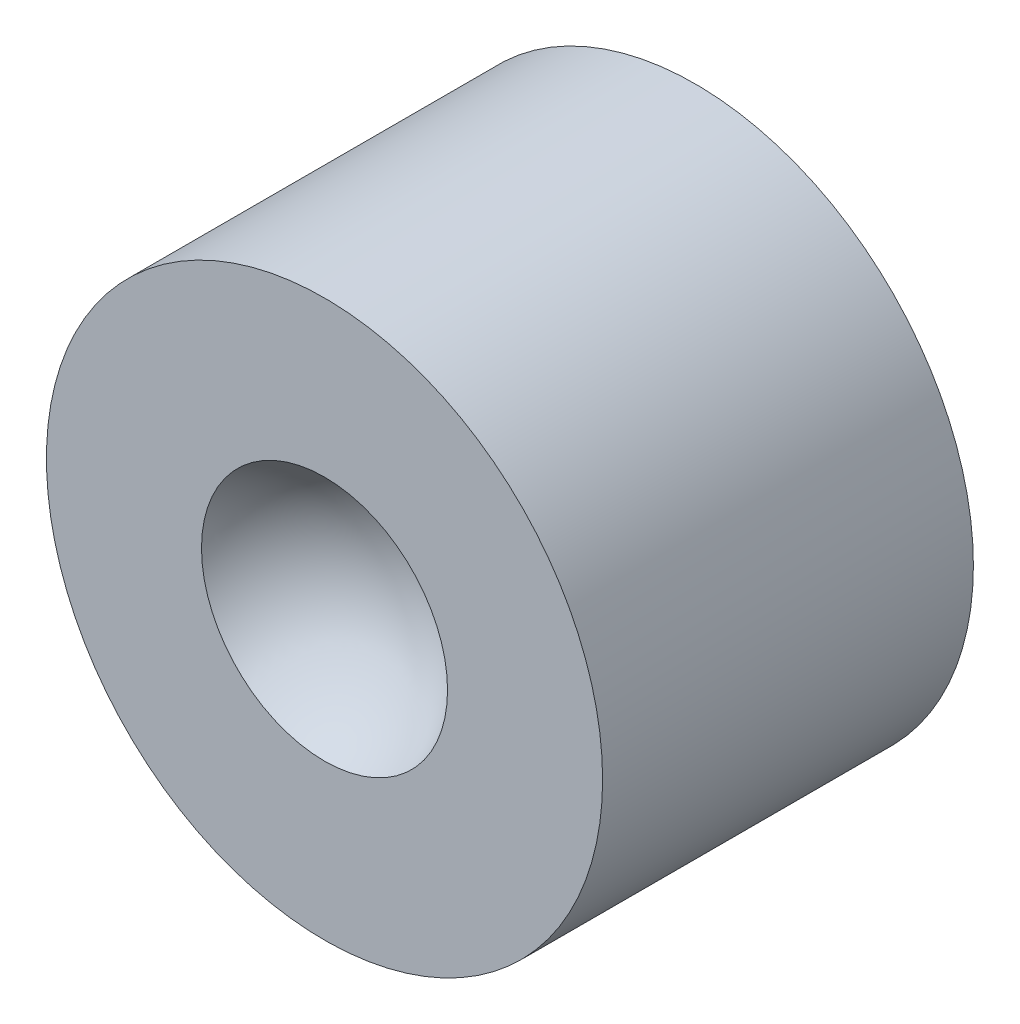
SolidWorks part; units mm, degrees
material "Brass"
ref_plane "Front Plane" through (0, 0, 0) normal (0, 0, 1) x (1, 0, 0)
ref_plane "Top Plane" through (0, 0, 0) normal (0, 1, 0) x (1, 0, 0)
ref_plane "Right Plane" through (0, 0, 0) normal (1, 0, 0) x (0, 0, -1)
sketch "Sketch1" plane through (0, 0, 0) normal (0, 0, 1) x (1, 0, 0)
  circle A0 centre (0, 0) radius 4.7625
  dimension "D1" = 9.525
extrude "Boss-Extrude1" add sketch "Sketch1" along normal blind 6.35
sketch "Sketch3" plane through (0, 0, 0) normal (0, 1, 0) x (1, 0, 0)
  line L0 (0, 0) -> (0, -6.721) construction
  line L1 (0, -6.35) -> (0, -5.08)
  line L2 (-4.7625, -6.35) -> (4.7625, -6.35) construction
  line L3 (2.1069, -6.35) -> (0, -6.35)
  arc A0 (0, -5.08) -> (2.1069, -6.35) centre (0.0009, -7.4612) cw
  dimension "D2" = 2.3813
  dimension "D1" = 1.27
  dimension "D3" = 2.1069
revolve "Cut-Revolve1" cut sketch "Sketch3" angle 360 about L0
